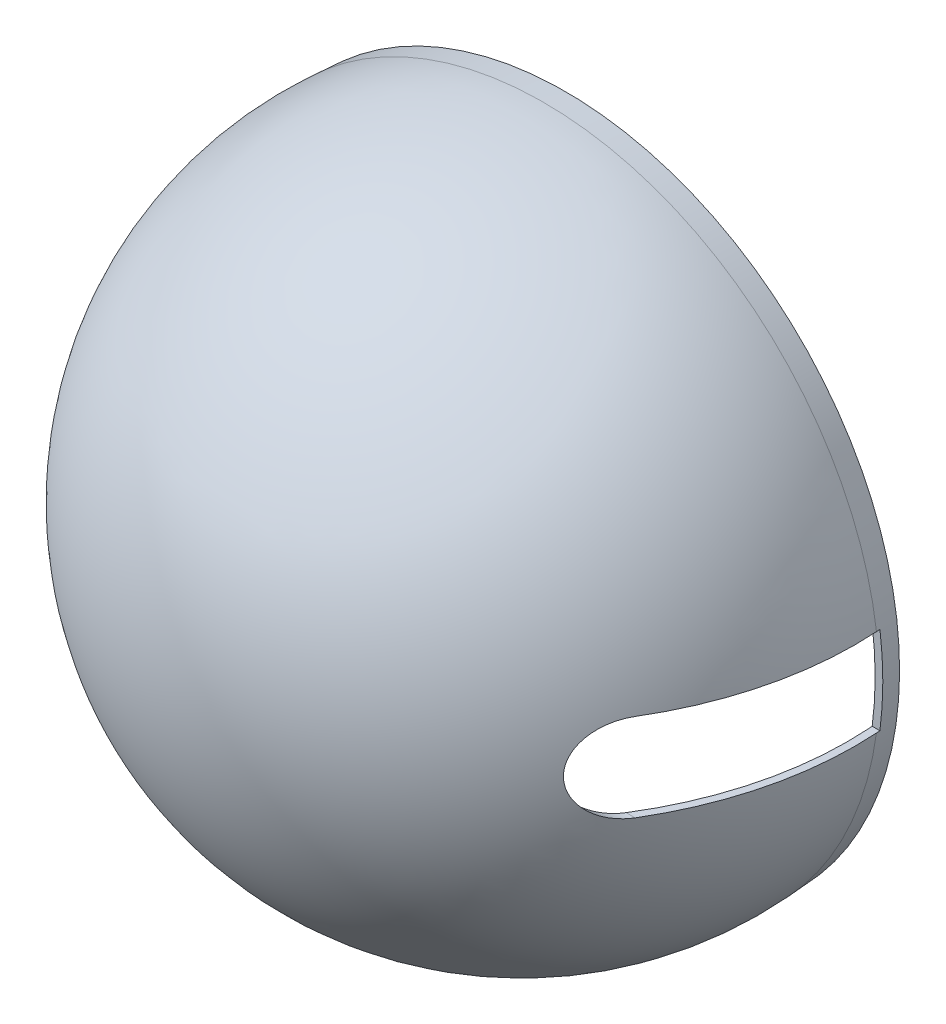
SolidWorks part; units mm, degrees
ref_plane "Front Plane" through (0, 0, 0) normal (0, 0, 1) x (1, 0, 0)
ref_plane "Top Plane" through (0, 0, 0) normal (0, 1, 0) x (1, 0, 0)
ref_plane "Right Plane" through (0, 0, 0) normal (1, 0, 0) x (0, 0, -1)
sketch "Sketch2" plane through (0, -7.3749, -7.41) normal (0, -1, 0) x (-1, 0, 0)
  line L0 (7.4, -5.41) -> (7.4, -21.272) construction
  line L1 (50.3393, -10.3126) -> (50.1494, -7.41)
  line L2 (5.025, -5.41) -> (9.775, -5.41) construction
  line L3 (50.1494, -7.41) -> (51.1515, -7.41)
  line L5 (51.1515, -7.41) -> (51.3371, -10.2473)
  line L6 (-30.4467, -7.41) -> (51.1558, -7.41) construction
  line L12 (7.4, -56.1534) -> (7.4, -57.1534)
  arc A4 (7.4, -56.1534) -> (50.3393, -10.3126) centre (7.4, -13.1223) ccw
  arc A5 (7.4, -57.1534) -> (51.3371, -10.2473) centre (7.4, -13.1223) ccw
  dimension "D2" = 1
revolve "Revolve1" add sketch "Sketch2" angle 360 about L0
sketch "Sketch3" plane through (0, 0, 0) normal (1, 0, 0) x (0, 0, -1)
  line L0 (-2.3481, -13.16) -> (-28.25, -13.16) construction
  line L2 (-28.25, -1.66) -> (-2.3481, -1.66) construction
  line L6 (-2.3481, -13.16) -> (-28.25, -13.16)
  line L8 (-28.25, -1.66) -> (-2.3481, -1.66)
  line L12 (-2.3481, -13.16) -> (-2.3481, -1.66)
  arc A10 (-28.25, -1.66) -> (-28.25, -13.16) centre (-28.25, -7.41) ccw
extrude "Cut-Extrude1" cut sketch "Sketch3" along normal through all
